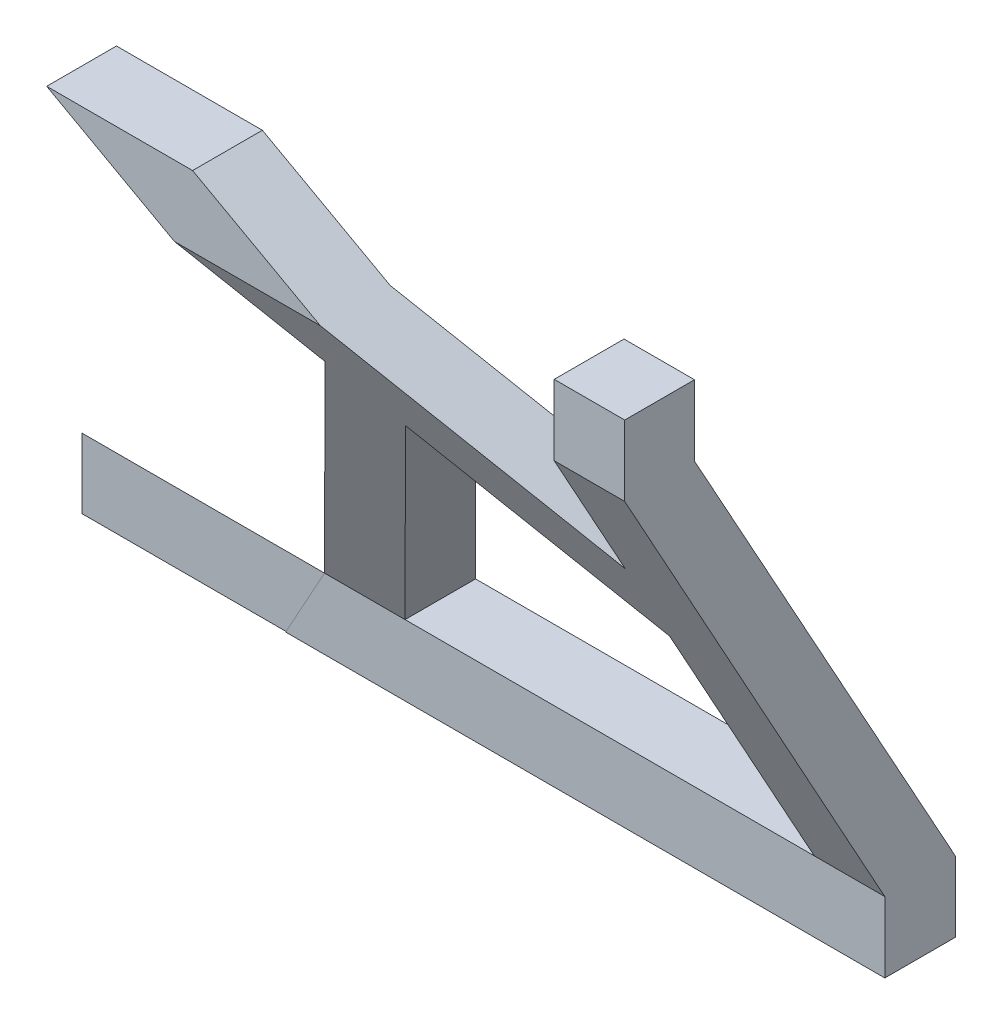
SolidWorks part; units mm, degrees
ref_plane "Płaszczyzna przednia" through (0, 0, 0) normal (0, 0, 1) x (1, 0, 0)
ref_plane "Płaszczyzna górna" through (0, 0, 0) normal (0, 1, 0) x (1, 0, 0)
ref_plane "Płaszczyzna prawa" through (0, 0, 0) normal (1, 0, 0) x (0, 0, -1)
sketch "Sketch1" plane through (0, 0, 0) normal (0, 0, 1) x (1, 0, 0)
  line L0 (99.7522, 182.6617) -> (122.7051, 97)
  line L1 (0, 0) -> (0, 300) construction
  line L2 (17.5495, 182.6617) -> (99.7522, 182.6617) construction
  line L3 (0, 239.8778) -> (60, 239.8778) construction
  line L4 (60, 239.8778) -> (80, 239.8778) construction
  line L5 (80, 239.8778) -> (80, 256.3778) construction
  line L6 (122.7051, 97) -> (122.7051, 93)
  line L7 (122.7051, 10) -> (122.7051, 0) construction
  line L8 (0, 0) -> (122.7051, 0) construction
  line L9 (109.4114, 185.2498) -> (132.7051, 98.3165)
  line L10 (122.7051, 93) -> (17.5495, 93)
  line L12 (122.7051, 87) -> (17.5495, 87)
  line L13 (80, 256.3778) -> (80, 87) construction
  line L14 (132.7051, 98.3165) -> (135.7374, 87) construction
  line L15 (143.0579, 98.3165) -> (146.0902, 87) construction
  line L16 (132.7051, 98.3165) -> (143.0579, 98.3165)
  line L17 (142.3644, 100.9047) -> (146.7917, 84.382) construction
  line L18 (143.0579, 98.3165) -> (148.0579, 98.3165) construction
  line L19 (148.0579, 98.3165) -> (148.0579, 87)
  line L20 (148.0579, 87) -> (122.7051, 87)
  line L21 (17.5495, 93) -> (17.5495, 87)
  line L22 (132.7051, 98.3165) -> (132.7051, 87) construction
  line L23 (122.7051, 97) -> (122.7051, 87) construction
  line L24 (17.5495, 93) -> (17.5495, 182.6617) construction
  line L25 (99.7522, 182.6617) -> (109.4114, 185.2498) construction
  line L30 (109.4114, 185.2498) -> (99.7522, 182.6617)
  line L31 (80, 256.3778) -> (122.7051, 97) construction
  line L32 (109.4114, 185.2498) -> (114.2411, 186.5439)
  line L33 (109.4114, 185.2498) -> (110.7055, 180.4202)
  line L34 (110.7055, 180.4202) -> (115.5352, 181.7143)
  line L35 (114.2411, 186.5439) -> (115.5352, 181.7143)
  line L36 (109.4114, 185.2498) -> (115.5352, 181.7143) construction
  line L37 (110.7055, 180.4202) -> (114.2411, 186.5439) construction
  line L38 (89.6593, 258.966) -> (132.7051, 98.3165) construction
  line L39 (132.7051, 98.3165) -> (137.1324, 81.7938) construction
  line L40 (122.7051, 93) -> (122.7051, 87) construction
  line L41 (132.7051, 87) -> (132.7051, 0)
  line L42 (132.7051, 87) -> (132.7051, 98.3165) construction
  line L44 (47.7051, 0) -> (132.7051, 0)
  line L49 (50.7051, 87) -> (85.2065, 67.9623)
  line L50 (122.7051, 47.2707) -> (122.7051, 10)
  line L52 (71.4037, 87) -> (122.7051, 58.692)
  line L53 (122.7051, 47.2707) -> (109.5023, 47.2707) construction
  line L56 (70.1733, 10) -> (40.8607, 10) construction
  line L57 (93.962, 63.131) -> (122.7051, 47.2707)
  line L58 (122.7051, 58.692) -> (122.7051, 87)
  line L59 (50.7051, 93) -> (50.7051, 87) construction
  line L60 (85.2065, 67.9623) -> (47.7051, 0)
  line L61 (122.7051, 10) -> (64.6445, 10)
  line L62 (64.6445, 10) -> (93.962, 63.131)
  line L63 (47.7051, 0) -> (40.8607, 0)
  line L64 (40.8607, 0) -> (50.7051, 87)
  arc A0 (143.0579, 98.3165) -> (148.0579, 98.3165) centre (145.5579, 98.3165) cw
  point P3 (17.5495, 177.6617)
  point P31 (112.4733, 183.4821)
  point P32 (122.7051, 90)
  dimension "D16" = 2.5
  dimension "D1" = 60
  dimension "D2" = 20
  dimension "D3" = 16.5
  dimension "D4" = 15
  dimension "D5" = 165
  dimension "D6" = 10
  dimension "D7" = 90
  dimension "D9" = 10
  dimension "D10" = 90
  dimension "D11" = 5
  dimension "D12" = 6
  dimension "D13" = 300
  dimension "D14" = 105.1556
  dimension "D15" = 5
  dimension "D17" = 182.6617
  dimension "D18" = 10
  dimension "D19" = 85
  dimension "D22" = 115.1556
  dimension "D23" = 82
  dimension "D20" = 10
  dimension "D24" = 10
  dimension "D25" = 10
  dimension "D26" = 16.9393
  dimension "D27" = 10
  dimension "D8" = 10
sketch "Sketch8" plane through (0, 0, 0) normal (0, 1, 0) x (1, 0, 0)
  line L0 (0, 0) -> (0, -64.45) construction
  line L1 (0, -64.45) -> (15.4472, -64.45) construction
  line L2 (47.7051, -74.45) -> (132.7051, -74.45)
  line L3 (47.7051, -74.45) -> (47.7051, -64.45)
  line L4 (47.7051, -64.45) -> (132.7051, -64.45)
  line L5 (132.7051, -74.45) -> (132.7051, -64.45)
  line L6 (47.7051, -74.45) -> (132.7051, -64.45) construction
  line L7 (47.7051, -64.45) -> (132.7051, -74.45) construction
  line L8 (47.7051, 0) -> (47.7051, -27.1481) construction
  line L9 (132.7051, 0) -> (132.7051, -19.275) construction
  point P7 (90.2051, -69.45)
  dimension "D1" = 64.45
  dimension "D2" = 10
extrude "Boss-Extrude4" add sketch "Sketch8" along normal blind 10
ref_plane "Plane5" through (0, 87, 0) normal (0, 1, 0) x (1, 0, 0)
sketch "Sketch9" plane through (0, 87, 0) normal (0, 1, 0) x (1, 0, 0)
  line L0 (50.7051, -37.45) -> (132.7051, -37.45) construction
  line L1 (50.7051, 0) -> (50.7051, -37.45) construction
  line L2 (132.7051, 0) -> (132.7051, -37.45) construction
  line L4 (50.7051, -37.45) -> (132.7051, -37.45)
  line L5 (50.7051, -37.45) -> (50.7051, -27.55)
  line L6 (50.7051, -27.55) -> (132.7051, -27.55)
  line L7 (132.7051, -37.45) -> (132.7051, -27.55)
  line L8 (50.7051, -37.45) -> (132.7051, -27.55) construction
  line L9 (50.7051, -27.55) -> (132.7051, -37.45) construction
  point P12 (91.7051, -32.5)
  dimension "D1" = 37.45
  dimension "D2" = 9.9
extrude "Boss-Extrude5" add sketch "Sketch9" against normal blind 10 separate body
loft "Loft1" add section face at (91.7051, 77, 32.5) section face at (90.2051, 10, 69.45)
extrude "Cut-Extrude2" cut sketch "Sketch1" against normal through all both and the other way through all contours L52 L58 L12 | L62 L61 L50 L57 | L63 L64 L49 L60
sketch "Sketch10" plane through (132.7051, 0, 0) normal (1, 0, 0) x (0, 0, -1)
  line L0 (-64.55, 9.9) -> (-64.55, 0)
  line L1 (-64.55, 0) -> (-74.45, 0)
  line L2 (-74.45, 0) -> (-64.55, 9.9)
  dimension "D1" = 9.9
  dimension "D2" = 9.9
extrude "Boss-Extrude6" add sketch "Sketch10" against normal blind 114
mirror "Mirror9" about plane through (0, 0, 0) normal (0, 0, 1) of bodies 111
delete or keep bodies "Body-Delete/Keep 8" type delete bodies bodies 111
